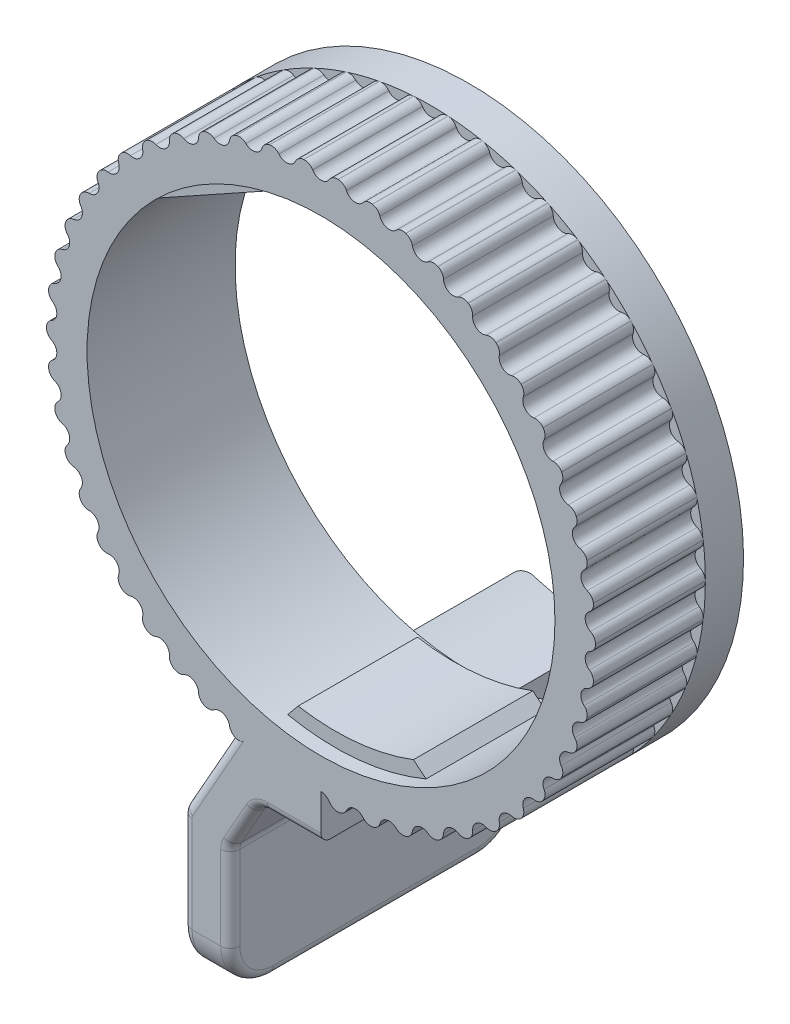
SolidWorks part; units mm, degrees
ref_plane "Plane1" through (0, 0, 0) normal (0, 0, 1) x (1, 0, 0)
ref_plane "Plane2" through (0, 0, 0) normal (0, 1, 0) x (1, 0, 0)
ref_plane "Plane3" through (0, 0, 0) normal (1, 0, 0) x (0, 0, -1)
sketch "Sketch1" plane through (0, 0, 0) normal (0, 0, 1) x (1, 0, 0)
  circle A0 centre (0, 0) radius 12.446
  circle A1 centre (0, 0) radius 14.605
  dimension "D1" = 24.892
  dimension "D2" = 29.21
extrude "Base-Extrude" add sketch "Sketch1" along normal mid plane 7.874
sketch "Sketch5" plane through (0, 0, 0) normal (0, 0, 1) x (1, 0, 0)
  line L0 (-2.032, 12.279) -> (-9.3578, 8.2058)
  line L1 (2.032, 12.279) -> (9.3578, 8.2058)
  circle A0 centre (0, 0) radius 12.446 construction
  arc A1 (9.3578, 8.2058) -> (2.032, 12.279) centre (0, 0) ccw
  arc A2 (-2.032, 12.279) -> (-9.3578, 8.2058) centre (0, 0) ccw
  dimension "D1" = 4.064
  dimension "D2" = 8.382
extrude "Boss-Extrude3" add sketch "Sketch5" along normal mid plane 6.35
sketch "Sketch9" plane through (0, 0, 0) normal (0, 0, 1) x (1, 0, 0)
  line L0 (-1.979, -11.5152) -> (-2.5311, -12.1859)
  line L1 (4.1553, -10.9201) -> (4.826, -11.4723)
  arc A0 (-2.5311, -12.1859) -> (4.826, -11.4723) centre (0, 0) ccw
  circle A1 centre (0, 0) radius 11.684
  arc A2 (-1.979, -11.5152) -> (4.1553, -10.9201) centre (0, 0) ccw
  circle A3 centre (0, 0) radius 12.446 construction
  dimension "D2" = 2.5311
  dimension "D3" = 4.826
  dimension "D1" = 0.762
extrude "Boss-Extrude6" add sketch "Sketch9" along normal mid plane 6.35
sketch "Sketch2" plane through (0, 0, 3.937) normal (0, 0, 1) x (1, 0, 0)
  line L0 (0, 0) -> (0, 14.605) construction
  arc A0 (-0.4446, 14.334) -> (0.4446, 14.334) centre (0, 14.605) ccw
  circle A1 centre (0, 0) radius 14.605 construction
  arc A2 (0.91, 14.5766) -> (-0.91, 14.5766) centre (0, 0) ccw
  arc A3 (-0.91, 14.5766) -> (-0.4446, 14.334) centre (-0.8784, 14.0696) cw
  arc A4 (0.91, 14.5766) -> (0.4446, 14.334) centre (0.8784, 14.0696) ccw
  dimension "D1" = 1.0414
  dimension "D2" = 0.508
extrude "Cut-Extrude1" cut sketch "Sketch2" against normal blind 5.842
pattern_circular "CirPattern1" count 50 every 7.2 about axis through (0, 0, 0) along (0, 0, 1) of "Cut-Extrude1"
sketch "Sketch6" plane through (0, 0, -3.937) normal (0, 0, -1) x (-1, 0, 0)
  line L0 (0, 0) -> (0, -12.446) construction
  line L1 (0, -12.446) -> (0, -16.51)
  line L2 (0, -16.51) -> (3.302, -16.51)
  line L3 (3.302, -16.51) -> (4.826, -19.2095)
  line L4 (4.826, -19.2095) -> (4.826, -26.162)
  line L5 (4.826, -26.162) -> (7.366, -26.162)
  line L6 (7.366, -26.162) -> (7.366, -18.542)
  line L7 (7.366, -18.542) -> (3.6206, -11.9077)
  arc A0 (0, -12.446) -> (3.6206, -11.9077) centre (0, 0) ccw
  circle A1 centre (0, 0) radius 12.446 construction
  dimension "D1" = 4.064
  dimension "D2" = 2.54
  dimension "D3" = 3.302
  dimension "D4" = 4.826
  dimension "D5" = 9.652
  dimension "D6" = 7.62
  dimension "D7" = 2.54
extrude "Boss-Extrude4" add sketch "Sketch6" against normal through all
sketch "Sketch7" plane through (0, 0, -3.937) normal (0, 0, -1) x (-1, 0, 0)
  line L7 (0, -14.605) -> (0, -16.51)
  line L8 (0, -16.51) -> (3.302, -16.51)
  line L9 (3.302, -16.51) -> (4.826, -19.2095)
  line L10 (4.826, -19.2095) -> (4.826, -26.162)
  line L11 (4.826, -26.162) -> (7.366, -26.162)
  line L12 (7.366, -26.162) -> (7.366, -18.542)
  line L13 (7.366, -18.542) -> (4.704, -13.8267)
  line L14 (0, -14.605) -> (0, -16.51)
  line L15 (0, -16.51) -> (3.302, -16.51)
  line L16 (3.302, -16.51) -> (4.826, -19.2095)
  line L17 (4.826, -19.2095) -> (4.826, -26.162)
  line L18 (4.826, -26.162) -> (7.366, -26.162)
  line L19 (7.366, -26.162) -> (7.366, -18.542)
  line L20 (7.366, -18.542) -> (4.704, -13.8267)
  arc A0 (0, -14.605) -> (4.704, -13.8267) centre (0, 0) ccw
  arc A1 (4.704, -13.8267) -> (0, -14.605) centre (0, 0) ccw
  arc A2 (4.704, -13.8267) -> (0, -14.605) centre (0, 0) ccw construction
  dimension "D1" = 0
extrude "Boss-Extrude5" add sketch "Sketch7" along normal blind 7.62
fillet "Fillet1" radius 2.286 2 edges at (-6.096, -26.162, 3.937) (-6.096, -26.162, -11.557)
fillet "Fillet2" radius 0.762 3 edges at (-3.302, -16.51, -3.81) (-4.826, -21.5427, -11.557) (-7.366, -18.542, -3.81)
fillet "Fillet5" radius 0.508 22 edges at (-1.4286, -16.51, 3.937) (-1.4286, -16.51, -11.557) (-7.366, -21.3091, -11.557) (-7.366, -26.162, -3.81) (-7.366, -21.3091, 3.937) (-7.366, -25.4924, 3.2674) (-7.366, -25.4924, -10.8874) (-4.826, -26.162, -3.81) (-4.826, -25.4924, 3.2674) (-4.826, -25.4924, -10.8874) (-4.1241, -17.9662, -11.557) (-4.1241, -17.9662, 3.937) (-4.826, -21.6429, -11.557) (-4.826, -21.6429, 3.937) (-5.9858, -16.0972, -11.557) (-7.341, -18.5486, -11.557) (-5.9771, -16.0819, 3.937) (-7.341, -18.5486, 3.937) (-3.2413, -16.6139, -11.557) (-3.2413, -16.6139, 3.937) (-4.801, -19.216, -11.557) (-4.801, -19.216, 3.937)
